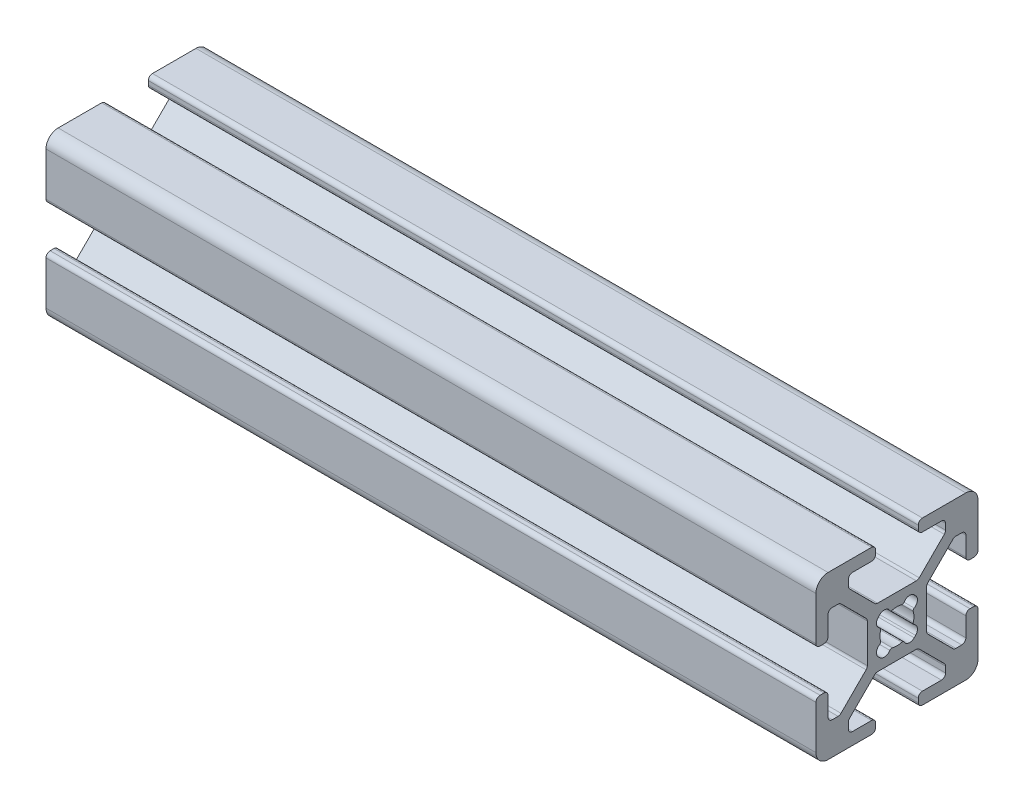
SolidWorks part; units mm, degrees
ref_plane "Front Plane" through (0, 0, 0) normal (0, 0, 1) x (1, 0, 0)
ref_plane "Top Plane" through (0, 0, 0) normal (0, 1, 0) x (1, 0, 0)
ref_plane "Right Plane" through (0, 0, 0) normal (1, 0, 0) x (0, 0, -1)
sketch "Sketch1" plane through (0, 0, 0) normal (0, 1, 0) x (1, 0, 0)
  line L0 (0, 0) -> (95, 0)
  dimension "D1" = 95
other "20_series 20-2020(1)"
ref_plane "Plane1" through (0, 0, 0) normal (1, 0, 0) x (0, 0, -1)
sketch "Sketch11" plane through (0, 0, 0) normal (1, 0, 0) x (0, 0, -1)
  line L0 (9.0094, 2.6289) -> (9.492, 2.6289)
  line L1 (8.5014, 5.4864) -> (8.5014, 3.1369)
  line L2 (10, 8.5014) -> (10, 3.1369)
  line L3 (7.2645, 5.9944) -> (7.9934, 5.9944)
  line L4 (3.1369, 10) -> (8.5014, 10)
  line L5 (3.8074, 2.7477) -> (6.9053, 5.8456)
  line L6 (2.6289, 9.0094) -> (2.6289, 9.492)
  line L7 (3.6586, -2.3885) -> (3.6586, 2.3885)
  line L8 (3.1369, 8.5014) -> (5.4864, 8.5014)
  line L9 (6.9053, -5.8456) -> (3.8074, -2.7477)
  line L10 (5.9944, 7.9934) -> (5.9944, 7.2645)
  line L11 (7.9934, -5.9944) -> (7.2645, -5.9944)
  line L12 (5.8456, 6.9053) -> (2.7477, 3.8074)
  line L13 (8.5014, -3.1369) -> (8.5014, -5.4864)
  line L14 (2.3885, 3.6586) -> (-2.3885, 3.6586)
  line L15 (9.0094, -2.6289) -> (9.492, -2.6289)
  line L16 (-2.7477, 3.8074) -> (-5.8456, 6.9053)
  line L17 (10, -3.1369) -> (10, -8.5014)
  line L18 (-5.9944, 7.2645) -> (-5.9944, 7.9934)
  line L19 (8.5014, -10) -> (3.1369, -10)
  line L20 (-5.4864, 8.5014) -> (-3.1369, 8.5014)
  line L21 (2.6289, -9.0094) -> (2.6289, -9.492)
  line L22 (-2.6289, 9.0094) -> (-2.6289, 9.492)
  line L23 (5.4864, -8.5014) -> (3.1369, -8.5014)
  line L24 (-8.5014, 10) -> (-3.1369, 10)
  line L25 (5.9944, -7.2645) -> (5.9944, -7.9934)
  line L26 (-10, 3.1369) -> (-10, 8.5014)
  line L27 (2.7477, -3.8074) -> (5.8456, -6.9053)
  line L28 (-9.0094, 2.6289) -> (-9.492, 2.6289)
  line L29 (-2.3885, -3.6586) -> (2.3885, -3.6586)
  line L30 (-8.5014, 3.1369) -> (-8.5014, 5.4864)
  line L31 (-5.8456, -6.9053) -> (-2.7477, -3.8074)
  line L32 (-7.9934, 5.9944) -> (-7.2645, 5.9944)
  line L33 (-5.9944, -7.9934) -> (-5.9944, -7.2645)
  line L34 (-6.9053, 5.8456) -> (-3.8074, 2.7477)
  line L35 (-3.1369, -8.5014) -> (-5.4864, -8.5014)
  line L36 (-3.6586, 2.3885) -> (-3.6586, -2.3885)
  line L37 (-2.6289, -9.0094) -> (-2.6289, -9.492)
  line L38 (-3.8074, -2.7477) -> (-6.9053, -5.8456)
  line L39 (-3.1369, -10) -> (-8.5014, -10)
  line L40 (-7.2645, -5.9944) -> (-7.9934, -5.9944)
  line L41 (-10, -8.5014) -> (-10, -3.1369)
  line L42 (-8.5014, -5.4864) -> (-8.5014, -3.1369)
  line L43 (-9.0094, -2.6289) -> (-9.492, -2.6289)
  line L44 (-2.2966, 2.1217) -> (-2.1217, 2.2966)
  line L45 (2.1217, 2.2966) -> (2.2966, 2.1217)
  line L46 (-2.1217, -2.2966) -> (-2.2966, -2.1217)
  line L47 (2.2966, -2.1217) -> (2.1217, -2.2966)
  arc A0 (8.5014, 3.1369) -> (9.0094, 2.6289) centre (9.0094, 3.1369) ccw
  arc A1 (9.492, 2.6289) -> (10, 3.1369) centre (9.492, 3.1369) ccw
  arc A2 (8.5014, 5.4864) -> (7.9934, 5.9944) centre (7.9934, 5.4864) ccw
  arc A3 (10, 8.5014) -> (8.5014, 10) centre (8.5014, 8.5014) ccw
  arc A4 (7.2645, 5.9944) -> (6.9053, 5.8456) centre (7.2645, 5.4864) ccw
  arc A5 (3.1369, 10) -> (2.6289, 9.492) centre (3.1369, 9.492) ccw
  arc A6 (3.8074, 2.7477) -> (3.6586, 2.3885) centre (4.1666, 2.3885) ccw
  arc A7 (2.6289, 9.0094) -> (3.1369, 8.5014) centre (3.1369, 9.0094) ccw
  arc A8 (3.6586, -2.3885) -> (3.8074, -2.7477) centre (4.1666, -2.3885) ccw
  arc A9 (5.9944, 7.9934) -> (5.4864, 8.5014) centre (5.4864, 7.9934) ccw
  arc A10 (6.9053, -5.8456) -> (7.2645, -5.9944) centre (7.2645, -5.4864) ccw
  arc A11 (5.8456, 6.9053) -> (5.9944, 7.2645) centre (5.4864, 7.2645) ccw
  arc A12 (7.9934, -5.9944) -> (8.5014, -5.4864) centre (7.9934, -5.4864) ccw
  arc A13 (2.3885, 3.6586) -> (2.7477, 3.8074) centre (2.3885, 4.1666) ccw
  arc A14 (9.0094, -2.6289) -> (8.5014, -3.1369) centre (9.0094, -3.1369) ccw
  arc A15 (-2.7477, 3.8074) -> (-2.3885, 3.6586) centre (-2.3885, 4.1666) ccw
  arc A16 (10, -3.1369) -> (9.492, -2.6289) centre (9.492, -3.1369) ccw
  arc A17 (-5.9944, 7.2645) -> (-5.8456, 6.9053) centre (-5.4864, 7.2645) ccw
  arc A18 (8.5014, -10) -> (10, -8.5014) centre (8.5014, -8.5014) ccw
  arc A19 (-5.4864, 8.5014) -> (-5.9944, 7.9934) centre (-5.4864, 7.9934) ccw
  arc A20 (2.6289, -9.492) -> (3.1369, -10) centre (3.1369, -9.492) ccw
  arc A21 (-3.1369, 8.5014) -> (-2.6289, 9.0094) centre (-3.1369, 9.0094) ccw
  arc A22 (3.1369, -8.5014) -> (2.6289, -9.0094) centre (3.1369, -9.0094) ccw
  arc A23 (-2.6289, 9.492) -> (-3.1369, 10) centre (-3.1369, 9.492) ccw
  arc A24 (5.4864, -8.5014) -> (5.9944, -7.9934) centre (5.4864, -7.9934) ccw
  arc A25 (-8.5014, 10) -> (-10, 8.5014) centre (-8.5014, 8.5014) ccw
  arc A26 (5.9944, -7.2645) -> (5.8456, -6.9053) centre (5.4864, -7.2645) ccw
  arc A27 (-10, 3.1369) -> (-9.492, 2.6289) centre (-9.492, 3.1369) ccw
  arc A28 (2.7477, -3.8074) -> (2.3885, -3.6586) centre (2.3885, -4.1666) ccw
  arc A29 (-9.0094, 2.6289) -> (-8.5014, 3.1369) centre (-9.0094, 3.1369) ccw
  arc A30 (-2.3885, -3.6586) -> (-2.7477, -3.8074) centre (-2.3885, -4.1666) ccw
  arc A31 (-7.9934, 5.9944) -> (-8.5014, 5.4864) centre (-7.9934, 5.4864) ccw
  arc A32 (-5.8456, -6.9053) -> (-5.9944, -7.2645) centre (-5.4864, -7.2645) ccw
  arc A33 (-6.9053, 5.8456) -> (-7.2645, 5.9944) centre (-7.2645, 5.4864) ccw
  arc A34 (-5.9944, -7.9934) -> (-5.4864, -8.5014) centre (-5.4864, -7.9934) ccw
  arc A35 (-3.6586, 2.3885) -> (-3.8074, 2.7477) centre (-4.1666, 2.3885) ccw
  arc A36 (-2.6289, -9.0094) -> (-3.1369, -8.5014) centre (-3.1369, -9.0094) ccw
  arc A37 (-3.8074, -2.7477) -> (-3.6586, -2.3885) centre (-4.1666, -2.3885) ccw
  arc A38 (-3.1369, -10) -> (-2.6289, -9.492) centre (-3.1369, -9.492) ccw
  arc A39 (-7.2645, -5.9944) -> (-6.9053, -5.8456) centre (-7.2645, -5.4864) ccw
  arc A40 (-10, -8.5014) -> (-8.5014, -10) centre (-8.5014, -8.5014) ccw
  arc A41 (-8.5014, -5.4864) -> (-7.9934, -5.9944) centre (-7.9934, -5.4864) ccw
  arc A42 (-9.492, -2.6289) -> (-10, -3.1369) centre (-9.492, -3.1369) ccw
  arc A43 (-8.5014, -3.1369) -> (-9.0094, -2.6289) centre (-9.0094, -3.1369) ccw
  arc A44 (-0.8806, 2.1293) -> (-0.5885, 2.0112) centre (-0.6599, 2.2549) ccw
  arc A45 (0.5885, 2.0112) -> (-0.5885, 2.0112) centre (0, 0) ccw
  arc A46 (-0.8806, 2.1293) -> (-2.1217, 2.2966) centre (-1.565, 1.7398) ccw
  arc A47 (0.5885, 2.0112) -> (0.8806, 2.1293) centre (0.6599, 2.2549) ccw
  arc A48 (2.1217, 2.2966) -> (0.8806, 2.1293) centre (1.565, 1.7398) ccw
  arc A49 (-2.2966, 2.1217) -> (-2.1293, 0.8806) centre (-1.7398, 1.565) ccw
  arc A50 (-2.0112, 0.5885) -> (-2.1293, 0.8806) centre (-2.2549, 0.6599) ccw
  arc A51 (2.1293, 0.8806) -> (2.2966, 2.1217) centre (1.7398, 1.565) ccw
  arc A52 (-2.0112, 0.5885) -> (-2.0112, -0.5885) centre (0, 0) ccw
  arc A53 (2.1293, 0.8806) -> (2.0112, 0.5885) centre (2.2549, 0.6599) ccw
  arc A54 (-2.1293, -0.8806) -> (-2.0112, -0.5885) centre (-2.2549, -0.6599) ccw
  arc A55 (2.0112, -0.5885) -> (2.0112, 0.5885) centre (0, 0) ccw
  arc A56 (-2.1293, -0.8806) -> (-2.2966, -2.1217) centre (-1.7398, -1.565) ccw
  arc A57 (2.0112, -0.5885) -> (2.1293, -0.8806) centre (2.2549, -0.6599) ccw
  arc A58 (2.2966, -2.1217) -> (2.1293, -0.8806) centre (1.7398, -1.565) ccw
  arc A59 (-2.1217, -2.2966) -> (-0.8806, -2.1293) centre (-1.565, -1.7398) ccw
  arc A60 (-0.5885, -2.0112) -> (-0.8806, -2.1293) centre (-0.6599, -2.2549) ccw
  arc A61 (0.8806, -2.1293) -> (2.1217, -2.2966) centre (1.565, -1.7398) ccw
  arc A62 (-0.5885, -2.0112) -> (0.5885, -2.0112) centre (0, 0) ccw
  arc A63 (0.8806, -2.1293) -> (0.5885, -2.0112) centre (0.6599, -2.2549) ccw
  point P0 (0, 0)
